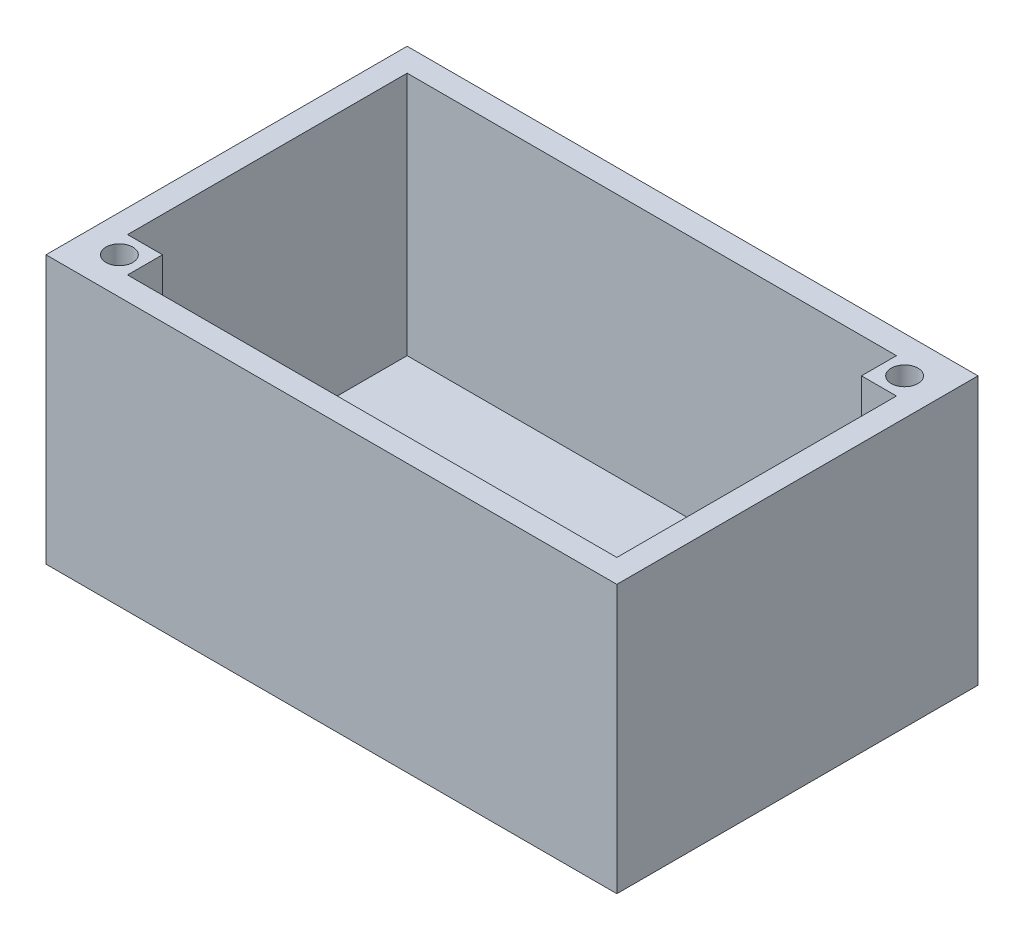
SolidWorks part; units mm, degrees
ref_plane "Front Plane" through (0, 0, 0) normal (0, 0, 1) x (1, 0, 0)
ref_plane "Top Plane" through (0, 0, 0) normal (0, 1, 0) x (1, 0, 0)
ref_plane "Right Plane" through (0, 0, 0) normal (1, 0, 0) x (0, 0, -1)
sketch "Sketch1" plane through (0, 0, 0) normal (0, 0, 1) x (1, 0, 0)
  line L1 (0, 0) -> (62.23, 0)
  line L2 (0, 0) -> (0, 29.21)
  line L3 (0, 29.21) -> (62.23, 29.21)
  line L4 (62.23, 0) -> (62.23, 29.21)
  dimension "D1" = 29.21
  dimension "D2" = 62.23
extrude "Boss-Extrude1" add sketch "Sketch1" against normal blind 39.37
shell "Shell1" thickness 2.54
sketch "Sketch2" plane through (0, 29.21, 0) normal (0, 1, 0) x (1, 0, 0)
  line L0 (6.35, 0) -> (6.35, 6.35)
  line L1 (0, 39.37) -> (0, 0) construction
  line L2 (62.23, 0) -> (0, 0) construction
  line L3 (0, 19.685) -> (62.23, 19.685) construction
  line L5 (62.23, 39.37) -> (62.23, 0) construction
  line L7 (6.35, 6.35) -> (0, 6.35)
  line L8 (31.115, 39.37) -> (31.115, 0) construction
  line L9 (62.23, 39.37) -> (0, 39.37) construction
  line L10 (2.54, 2.54) -> (59.69, 2.54) construction
  line L11 (2.54, 36.83) -> (2.54, 2.54) construction
  line L12 (6.35, 39.37) -> (6.35, 33.02)
  line L13 (6.35, 33.02) -> (0, 33.02)
  line L14 (55.88, 33.02) -> (62.23, 33.02)
  line L15 (55.88, 39.37) -> (55.88, 33.02)
  circle A6 centre (4.0005, 4.0005) radius 1.4605
  circle A7 centre (4.0005, 35.3695) radius 1.4605
  circle A8 centre (58.2295, 35.3695) radius 1.4605
  line M8 (59.69, 36.83) -> (59.69, 2.54)
  line M9 (59.69, 2.54) -> (2.54, 2.54)
  line M10 (2.54, 2.54) -> (2.54, 36.83)
  line M11 (2.54, 36.83) -> (59.69, 36.83)
  dimension "D1" = 2.921
  dimension "D2" = 6.35
extrude "Boss-Extrude2" add sketch "Sketch2" against normal up to next contours A6 M10 M9 | A8 M8 M11 | A8 L15 L14 M11 M8 | A6 L0 L7 M9 M10
